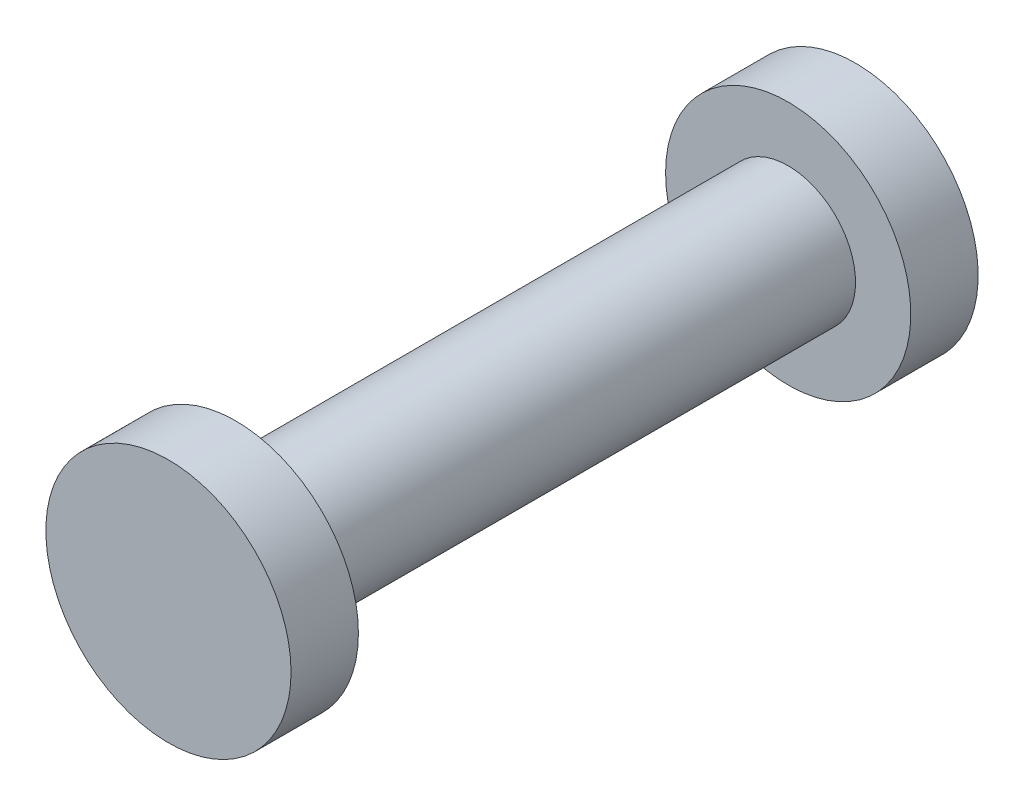
SolidWorks part; units mm, degrees
ref_plane "Front Plane" through (0, 0, 0) normal (0, 0, 1) x (1, 0, 0)
ref_plane "Top Plane" through (0, 0, 0) normal (0, 1, 0) x (1, 0, 0)
ref_plane "Right Plane" through (0, 0, 0) normal (1, 0, 0) x (0, 0, -1)
sketch "Sketch1" plane through (0, 0, 0) normal (0, 0, 1) x (1, 0, 0)
  circle A0 centre (0, 0) radius 0.5
  dimension "D1" = 1
extrude "Boss-Extrude1" add sketch "Sketch1" along normal blind 5.1
sketch "Sketch2" plane through (0, 0, 5.1) normal (0, 0, 1) x (1, 0, 0)
  circle A0 centre (0, 0) radius 0.91
  dimension "D1" = 1.82
extrude "Boss-Extrude2" add sketch "Sketch2" against normal blind 0.5
sketch "Sketch3" plane through (0, 0, 0) normal (0, 0, -1) x (-1, 0, 0)
  circle A0 centre (0, 0) radius 0.91
  circle A1 centre (0, 0) radius 0.91 construction
extrude "Boss-Extrude3" add sketch "Sketch3" against normal blind 0.5
